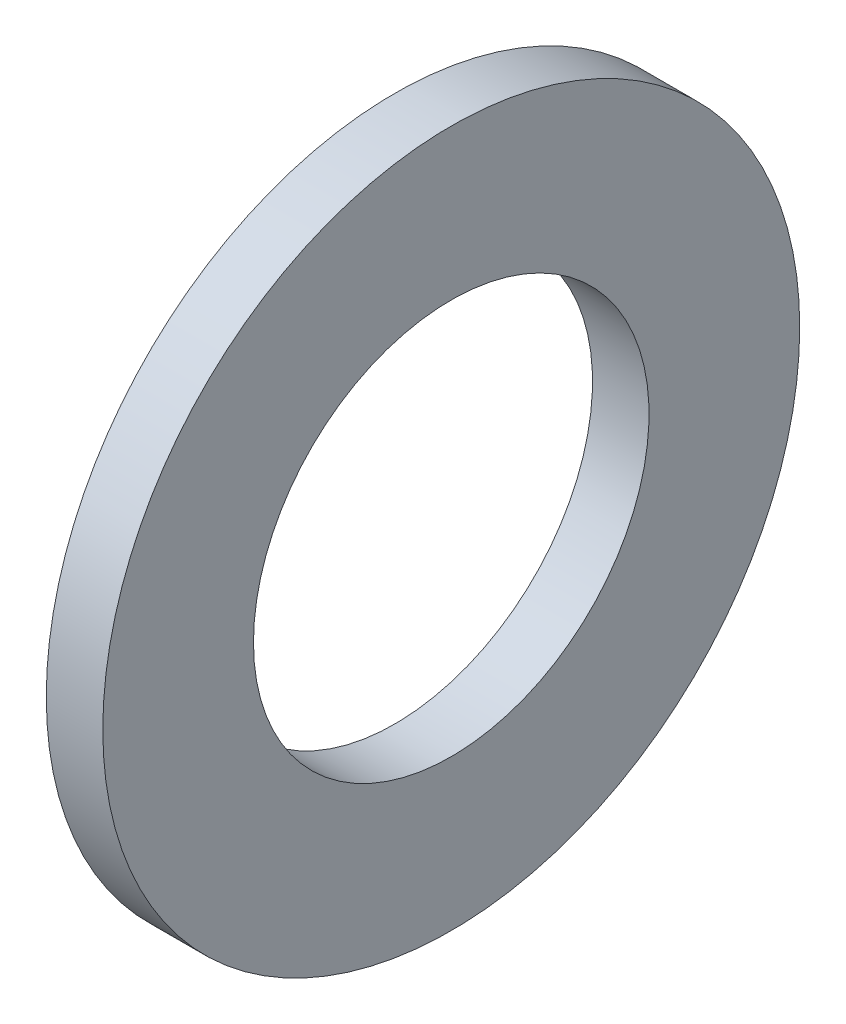
SolidWorks part; units mm, degrees
ref_plane "Plane1" through (0, 0, 0) normal (0, 0, 1) x (1, 0, 0)
ref_plane "Plane2" through (0, 0, 0) normal (0, 1, 0) x (1, 0, 0)
ref_plane "Plane3" through (0, 0, 0) normal (1, 0, 0) x (0, 0, -1)
sketch "Sketch1" plane through (0, 0, 0) normal (0, 0, 1) x (1, 0, 0)
  line L0 (-34.925, 0) -> (9.525, 0) construction
  line L1 (0, 10.5) -> (0, 18.5)
  line L2 (0, 18.5) -> (-3, 18.5)
  line L3 (-3, 18.5) -> (-3, 10.5)
  line L4 (-3, 10.5) -> (0, 10.5)
  dimension "Thickness" = 3
  dimension "Inside_dia" = 21
  dimension "Outside_dia" = 37
revolve "Base-Revolve" add sketch "Sketch1" angle 360 about L0
